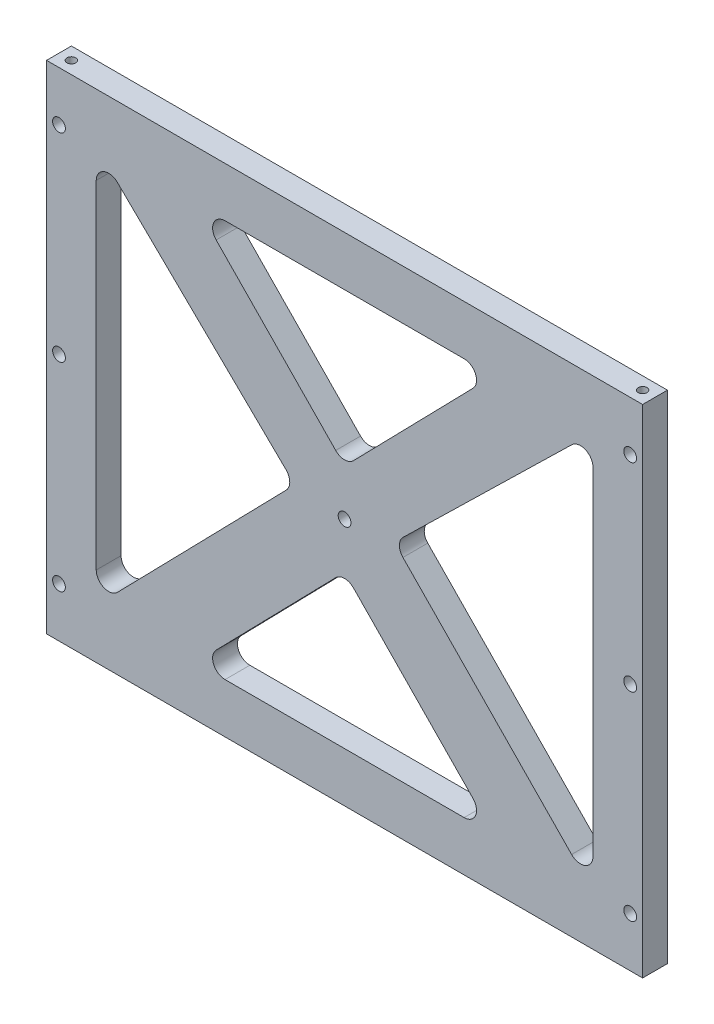
SolidWorks part; units mm, degrees
ref_plane "Front Plane" through (0, 0, 0) normal (0, 0, 1) x (1, 0, 0)
ref_plane "Top Plane" through (0, 0, 0) normal (0, 1, 0) x (1, 0, 0)
ref_plane "Right Plane" through (0, 0, 0) normal (1, 0, 0) x (0, 0, -1)
sketch "Sketch1" plane through (0, 0, 0) normal (0, 0, 1) x (1, 0, 0)
  line L1 (76.2, 63.5) -> (-76.2, 63.5)
  line L2 (76.2, 63.5) -> (76.2, -63.5)
  line L3 (76.2, -63.5) -> (-76.2, -63.5)
  line L4 (-76.2, 63.5) -> (-76.2, -63.5)
  line L5 (76.2, 63.5) -> (-76.2, -63.5) construction
  line L6 (76.2, -63.5) -> (-76.2, 63.5) construction
  point P0 (0, 0)
  dimension "D1" = 152.4
  dimension "D2" = 127
extrude "Boss-Extrude1" add sketch "Sketch1" along normal blind 6.35 contours L1 L4 L3 L2
ref_plane "Plane1" through (0, 0, 0) normal (-1, 0, 0) x (0, 0, 1)
ref_plane "Plane2" through (0, 0, 0) normal (0, 1, 0) x (1, 0, 0)
ref_plane "Plane3" through (0, 31.75, 0) normal (0, 1, 0) x (1, 0, 0)
ref_plane "Plane4" through (0, -31.75, 0) normal (0, 1, 0) x (1, 0, 0)
sketch "Sketch2" plane through (0, 0, 6.35) normal (0, 0, 1) x (1, 0, 0)
  line L6 (63.5, 50.8) -> (63.5, -50.8)
  line L56 (63.5, -50.8) -> (12.7, 1.2547)
  line L57 (12.7, 1.2547) -> (63.5, 50.8)
  line L58 (76.2, 63.5) -> (76.2, -63.5) construction
  line L59 (76.2, 63.5) -> (-76.2, 63.5) construction
  line L60 (76.2, -63.5) -> (-76.2, -63.5) construction
  line L61 (0, 3.4925) -> (0, -3.4925) construction
  line L62 (-63.5, -50.8) -> (-12.7, 1.2547)
  line L63 (-63.5, 50.8) -> (-63.5, -50.8)
  line L64 (-12.7, 1.2547) -> (-63.5, 50.8)
  line L65 (38.1, -50.8) -> (-38.1, -50.8)
  line L66 (-38.1, -50.8) -> (0, -11.7589)
  line L67 (0, -11.7589) -> (38.1, -50.8)
  line L68 (3.4925, 0) -> (-3.4925, 0) construction
  line L69 (-38.1, 50.8) -> (0, 11.7589)
  line L70 (38.1, 50.8) -> (-38.1, 50.8)
  line L71 (0, 11.7589) -> (38.1, 50.8)
  dimension "D1" = 12.7
  dimension "D2" = 12.7
  dimension "D3" = 12.7
  dimension "D4" = 12.7
  dimension "D5" = 25.4
  dimension "D6" = 25.4
  dimension "D7" = 0
  dimension "D8" = 180
extrude "Cut-Extrude1" cut sketch "Sketch2" against normal through all
hole_wizard "#4-40 Tapped Hole1" positions "Sketch7" profile "Sketch9" tap size "#4-40" standard "ANSI Inch"
sketch "Sketch7" plane through (0, -63.5, 0) normal (0, -1, 0) x (-1, 0, 0)
  line L0 (-76.2, -6.35) -> (-76.2, 0) construction
  line L1 (-76.2, -6.35) -> (76.2, -6.35) construction
  line L2 (0, -3.4925) -> (0, 3.4925) construction
  point P0 (-73.025, -3.175)
  point P9 (73.025, -3.175)
  dimension "D1" = 3.175
  dimension "D2" = 3.175
sketch "Sketch9" plane through (73.025, -63.5, 3.175) normal (1, 0, 0) x (0, 0, -1)
  line L0 (0, 0) -> (0, 8.2738)
  line L1 (0, 8.2738) -> (1.1303, 7.5946)
  line L2 (1.1303, 7.5946) -> (1.1303, 0)
  line L5 (1.1303, 0) -> (0, 0)
  line L10 (0, 8.2738) -> (-1.1303, 7.5946) construction
  line L11 (0, -6.35) -> (0, 107.95) construction
  dimension "Tap Drill Dia." = 2.2606
  dimension "Tap Drill Depth" = 7.5946
  dimension "Drill Angle" = 118
cosmetic thread "Hole Thread1" parameters "D1"=5.6896, "D2"=2.8448
cosmetic thread "Hole Thread2" parameters "D1"=5.6896, "D2"=2.8448
hole_wizard "CBORE for #4 Socket Head Cap Screw1" positions "Sketch10" profile "Sketch11" counterbore size "#4" standard "ANSI Inch"
sketch "Sketch10" plane through (0, 0, 0) normal (0, 0, -1) x (-1, 0, 0)
  line L0 (76.2, 63.5) -> (76.2, -63.5) construction
  line L3 (-76.2, 63.5) -> (76.2, 63.5) construction
  line L4 (0, -3.4925) -> (0, 3.4925) construction
  line L5 (3.4925, 0) -> (-3.4925, 0) construction
  point P0 (73.025, 0)
  point P2 (73.025, 50.8)
  point P15 (-73.025, 50.8)
  point P16 (-73.025, 0)
  point P20 (-73.025, -50.8)
  point P21 (73.025, -50.8)
  dimension "D1" = 3.175
  dimension "D2" = 3.175
  dimension "D3" = 12.7
sketch "Sketch11" plane through (-73.025, 0, 0) normal (1, 0, 0) x (0, 1, 0)
  line L0 (0, 0) -> (0, 8.5752)
  line L1 (0, 8.5752) -> (1.6319, 7.5946)
  line L2 (1.6319, 7.5946) -> (1.6319, 2.8448)
  line L3 (1.6319, 2.8448) -> (2.7788, 2.8448)
  line L4 (2.7788, 2.8448) -> (2.7788, 0)
  line L5 (2.7788, 0) -> (0, 0)
  line L10 (0, 8.5752) -> (-1.632, 7.5946) construction
  line L11 (0, -6.35) -> (0, 107.95) construction
  dimension "Hole Dia." = 3.2639
  dimension "Hole Depth" = 7.5946
  dimension "C'Bore Dia." = 5.5575
  dimension "C'Bore Depth" = 2.8448
  dimension "Drill Angle" = 118
hole_wizard "CBORE for #4 Socket Head Cap Screw2" positions "Sketch12" profile "Sketch13" counterbore size "#4" standard "ANSI Inch"
sketch "Sketch12" plane through (0, 0, 0) normal (0, 0, -1) x (-1, 0, 0)
  point P0 (0, 0)
sketch "Sketch13" plane through (0, 0, 0) normal (1, 0, 0) x (0, 1, 0)
  line L0 (0, 0) -> (0, 8.5752)
  line L1 (0, 8.5752) -> (1.6319, 7.5946)
  line L2 (1.6319, 7.5946) -> (1.6319, 2.8448)
  line L3 (1.6319, 2.8448) -> (2.7788, 2.8448)
  line L4 (2.7788, 2.8448) -> (2.7788, 0)
  line L5 (2.7788, 0) -> (0, 0)
  line L10 (0, 8.5752) -> (-1.632, 7.5946) construction
  line L11 (0, -6.35) -> (0, 107.95) construction
  dimension "Hole Dia." = 3.2639
  dimension "Hole Depth" = 7.5946
  dimension "C'Bore Dia." = 5.5575
  dimension "C'Bore Depth" = 2.8448
  dimension "Drill Angle" = 118
hole_wizard "#4-40 Tapped Hole2" positions "Sketch14" profile "Sketch15" tap size "#4-40" standard "ANSI Inch"
sketch "Sketch14" plane through (0, 63.5, 0) normal (0, 1, 0) x (1, 0, 0)
  line L0 (-76.2, -6.35) -> (-76.2, 0) construction
  line L1 (76.2, -6.35) -> (-76.2, -6.35) construction
  line L2 (0, 3.4925) -> (0, -3.4925) construction
  point P0 (-73.025, -3.175)
  point P15 (73.025, -3.175)
  dimension "D1" = 3.175
  dimension "D2" = 3.175
sketch "Sketch15" plane through (-73.025, 63.5, 3.175) normal (1, 0, 0) x (0, 0, 1)
  line L0 (0, 0) -> (0, 8.2738)
  line L1 (0, 8.2738) -> (1.1303, 7.5946)
  line L2 (1.1303, 7.5946) -> (1.1303, 0)
  line L5 (1.1303, 0) -> (0, 0)
  line L10 (0, 8.2738) -> (-1.1303, 7.5946) construction
  line L11 (0, -6.35) -> (0, 107.95) construction
  dimension "Tap Drill Dia." = 2.2606
  dimension "Tap Drill Depth" = 7.5946
  dimension "Drill Angle" = 118
cosmetic thread "Hole Thread3" parameters "D1"=6.9596, "D2"=2.8448
cosmetic thread "Hole Thread4" parameters "D1"=6.9596, "D2"=2.8448
fillet "Fillet1" radius 3.175 12 edges at (-63.5, -50.8, 3.175) (-63.5, 50.8, 3.175) (0, -11.7589, 3.175) (-38.1, 50.8, 3.175) (12.7, 1.2547, 3.175) (-38.1, -50.8, 3.175) (0, 11.7589, 3.175) (63.5, -50.8, 3.175) (38.1, -50.8, 3.175) (38.1, 50.8, 3.175) (-12.7, 1.2547, 3.175) (63.5, 50.8, 3.175)
